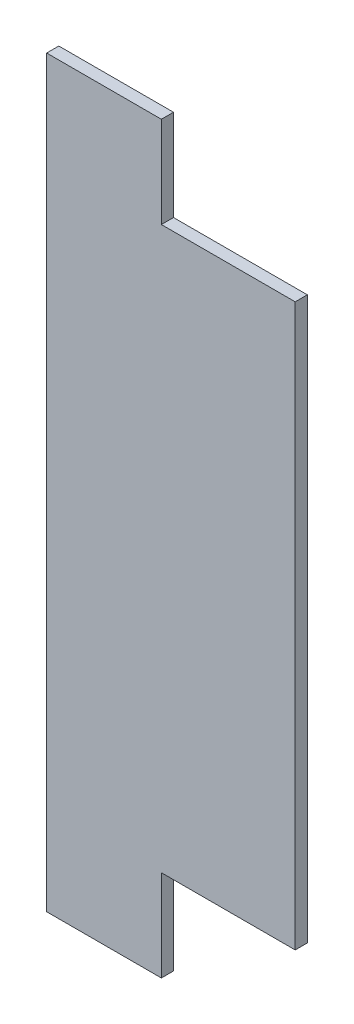
SolidWorks part; units mm, degrees
ref_plane "Front Plane" through (0, 0, 0) normal (0, 0, 1) x (1, 0, 0)
ref_plane "Top Plane" through (0, 0, 0) normal (0, 1, 0) x (1, 0, 0)
ref_plane "Right Plane" through (0, 0, 0) normal (1, 0, 0) x (0, 0, -1)
sketch "Sketch1" plane through (0, 0, 0) normal (0, 0, 1) x (1, 0, 0)
  line L0 (-15, 97.25) -> (15, -97.25) construction
  line L1 (-15, 97.25) -> (15, 97.25)
  line L2 (-15, 97.25) -> (-15, -97.25)
  line L3 (-15, -97.25) -> (15, -97.25)
  line L4 (15, 97.25) -> (15, -97.25)
  dimension "D1" = 30
  dimension "D2" = 194.5
extrude "Boss-Extrude1" add sketch "Sketch1" along normal blind 3.175
sketch "Sketch2" plane through (0, 0, 3.175) normal (0, 0, 1) x (1, 0, 0)
  line L0 (15, -97.25) -> (15, 97.25) construction
  line L1 (15, 73.4) -> (50, 73.4)
  line L2 (15, 73.4) -> (15, -73.4)
  line L3 (15, -73.4) -> (50, -73.4)
  line L4 (50, 73.4) -> (50, -73.4)
  line L5 (0, 0) -> (15, 0) construction
  line L6 (15, 97.25) -> (-15, 97.25) construction
  dimension "D1" = 23.85
  dimension "D2" = 35
extrude "Boss-Extrude2" add sketch "Sketch2" against normal up to surface (3.175 mm away) up to face at (0, 0, 0)
